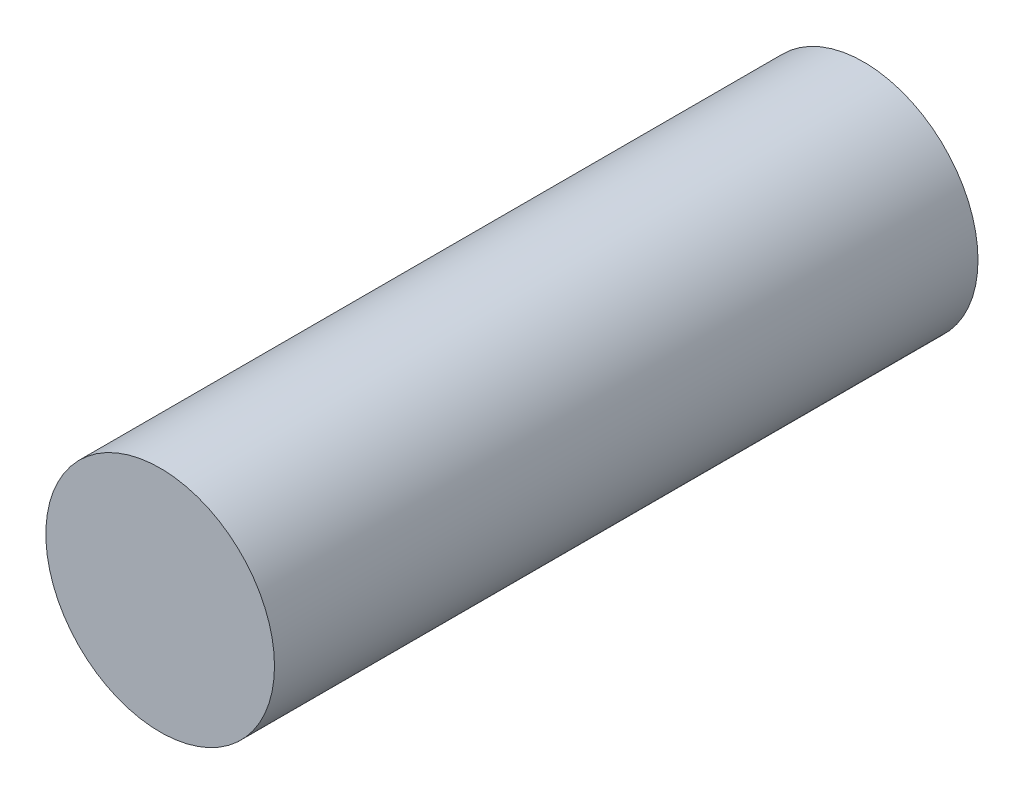
SolidWorks part; units mm, degrees
ref_plane "前视基准面" through (0, 0, 0) normal (0, 0, 1) x (1, 0, 0)
ref_plane "上视基准面" through (0, 0, 0) normal (0, 1, 0) x (1, 0, 0)
ref_plane "右视基准面" through (0, 0, 0) normal (1, 0, 0) x (0, 0, -1)
sketch "草图1" plane through (0, 0, 0) normal (0, 0, 1) x (1, 0, 0)
  circle A0 centre (0, 0) radius 4.875
  dimension "D1" = 9.75
extrude "凸台-拉伸1" add sketch "草图1" along normal blind 30
